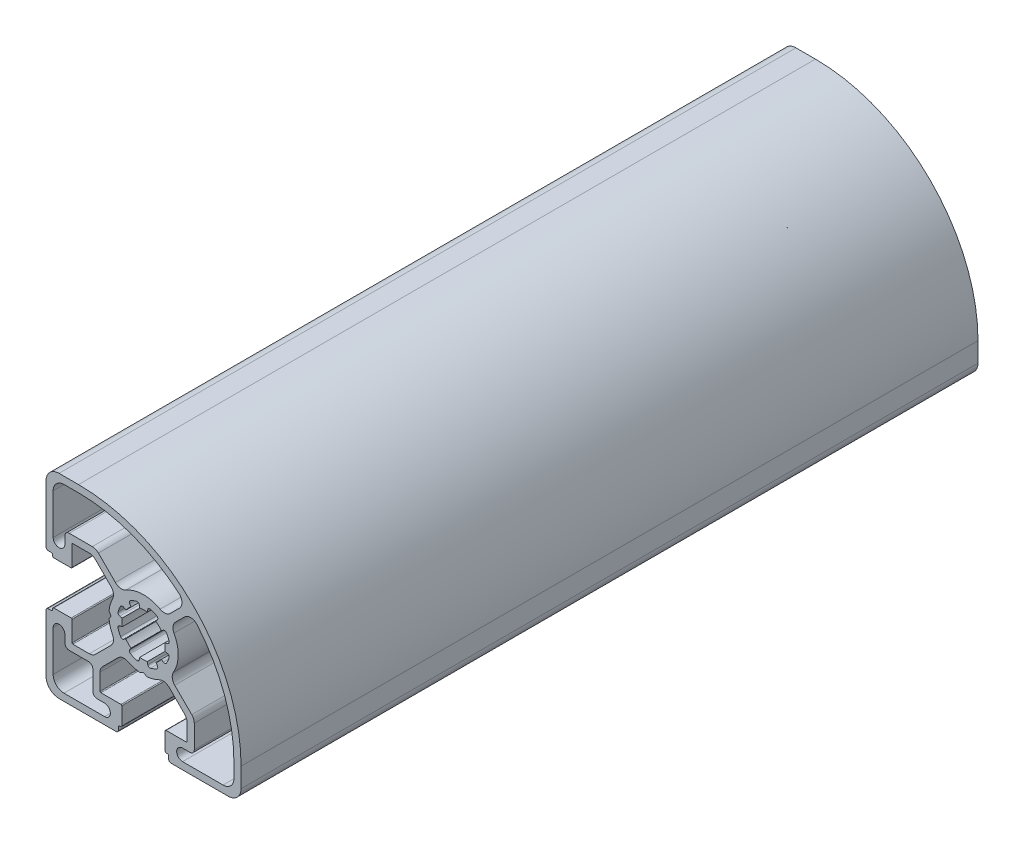
SolidWorks part; units mm, degrees
ref_plane "Front Plane" through (0, 0, 0) normal (0, 0, 1) x (1, 0, 0)
ref_plane "Top Plane" through (0, 0, 0) normal (0, 1, 0) x (1, 0, 0)
ref_plane "Right Plane" through (0, 0, 0) normal (1, 0, 0) x (0, 0, -1)
sketch "Sketch5" plane through (0, 0, 0) normal (0, 0, 1) x (1, 0, 0)
  line L0 (9.4354, 8.2687) -> (7.3664, 6.1997)
  line L1 (-22.5, 19.5) -> (-22.5, 6.3)
  line L2 (-6.493, 7.2001) -> (-10.4071, 11.1142)
  line L3 (-7.5243, 5.8979) -> (-11.0906, 9.4642)
  line L4 (-16.5, 9.85) -> (-16.5, 5.2)
  line L5 (-0.1368, -7.5833) -> (-0.7414, -7.9323)
  line L6 (-20.85, -18.35) -> (-20.85, -9)
  line L7 (-22.5, -19.5) -> (-22.5, -6.3)
  line L8 (-11.7, -17.15) -> (-11.7, -12.7)
  line L9 (-10.0399, -16.3101) -> (-10.0399, -12.5153)
  line L10 (-18.35, -20.85) -> (-9, -20.85)
  line L11 (-19.5, -22.5) -> (-6.3, -22.5)
  line L12 (-10.7, -18.15) -> (-9, -18.15)
  line L13 (-5.5, -21) -> (-5.3, -21)
  line L14 (-9.8399, -16.5101) -> (-5.2, -16.5101)
  line L15 (-5, -16.7101) -> (-5, -20.7)
  line L16 (-5.8, -22) -> (-5.8, -21.3)
  line L17 (-43.9952, 0) -> (43.9952, 0) construction
  line L18 (-18.15, -10.7) -> (-18.15, -9)
  line L19 (-21, -5.5) -> (-21, -5.3)
  line L20 (-16.7, -5) -> (-20.7, -5)
  line L21 (-16.5, -9.85) -> (-16.5, -5.2)
  line L22 (-22, -5.8) -> (-21.3, -5.8)
  line L23 (-16.3, -10.05) -> (-12.5048, -10.05)
  line L24 (-17.15, -11.7) -> (-12.7, -11.7)
  line L25 (0, 46.4479) -> (0, -46.4479) construction
  line L26 (-5.8876, -7.5346) -> (-9.4541, -11.1011)
  line L27 (-7.5243, -5.8979) -> (-11.0906, -9.4642)
  line L28 (-21, 5.3) -> (-21, 5.5)
  line L29 (-16.7, 5) -> (-20.7, 5)
  line L30 (-22, 5.8) -> (-21.3, 5.8)
  line L31 (0, 0) -> (23.3972, 0) construction
  line L32 (0, 0) -> (0, 22.9384) construction
  line L33 (0.0005, 0.0004) -> (0, 0) construction
  line L34 (-7.5577, -0.1) -> (-7.9277, -0.7409)
  line L35 (-7.5577, 0.1) -> (-7.9277, 0.7409)
  line L36 (0.0001, -0.0014) -> (0.0004, -0.001) construction
  line L37 (0.0001, -0.0002) -> (0, 0) construction
  line L38 (0.0003, -0.0003) -> (0.0001, -0.0002) construction
  line L39 (22.5, -19.5) -> (22.5, -15)
  line L40 (10.0399, -16.3101) -> (10.0399, -12.5153)
  line L41 (11.7, -17.15) -> (11.7, -11.8213)
  line L42 (20.85, -18.35) -> (20.85, -15)
  line L43 (18.35, -20.85) -> (9, -20.85)
  line L44 (10.7, -18.15) -> (9, -18.15)
  line L45 (19.5, -22.5) -> (6.3, -22.5)
  line L46 (5.3, -21.0103) -> (5.5, -21.0103)
  line L47 (9.8399, -16.5101) -> (5.2, -16.5101)
  line L48 (5, -16.7101) -> (5, -20.7103)
  line L49 (5.8, -22) -> (5.8, -21.3103)
  line L50 (0.0001, -0.0014) -> (0.0003, -0.0015) construction
  line L51 (7.2001, -6.493) -> (11.1142, -10.4071)
  line L52 (0.0632, -7.5833) -> (0.7407, -7.9744)
  line L53 (-0.8683, 4.924) -> (-0.9686, 5.4929)
  line L54 (5.9187, -7.5657) -> (9.4541, -11.1011)
  line L55 (-4.0956, 2.868) -> (-4.5688, 3.1993)
  line L56 (-2.8679, 4.0958) -> (-3.1992, 4.5689)
  line L57 (-4.924, 0.8682) -> (-5.4928, 0.9685)
  line L58 (-0.0005, -0.0004) -> (0, 0) construction
  line L59 (-0.0001, -0.0003) -> (-0.0004, -0.0007) construction
  line L60 (-0.0001, -0.0015) -> (0, -0.0017) construction
  line L61 (-20.85, 18.35) -> (-20.85, 9)
  line L62 (-18.15, 10.7) -> (-18.15, 9)
  line L63 (-17.15, 11.7) -> (-11.8213, 11.7)
  line L64 (-16.3, 10.05) -> (-12.5048, 10.05)
  line L65 (-19.5, 22.5) -> (-15, 22.5)
  line L66 (-18.35, 20.85) -> (-15, 20.85)
  line L67 (8.2687, 9.4354) -> (6.1997, 7.3664)
  line L68 (-0.0003, -0.0014) -> (-0.0001, -0.0015) construction
  line L69 (-0.0001, -0.0003) -> (-0.0003, -0.0002) construction
  line L70 (0.0001, -0.0003) -> (0.0003, -0.0002) construction
  line L71 (0.0003, -0.0014) -> (0.0001, -0.0015) construction
  line L72 (0.0001, -0.0015) -> (0, -0.0017) construction
  line L73 (0.0001, -0.0003) -> (0.0004, -0.0007) construction
  line L74 (0.0005, -0.0004) -> (0, 0) construction
  line L75 (0.8683, -4.924) -> (0.9686, -5.4929)
  line L76 (4.0956, -2.868) -> (4.5688, -3.1993)
  line L77 (-0.0001, -0.0014) -> (-0.0003, -0.0015) construction
  line L78 (-0.0003, -0.0003) -> (-0.0001, -0.0002) construction
  line L79 (2.8679, -4.0958) -> (3.1992, -4.5689)
  line L80 (4.924, -0.8682) -> (5.4928, -0.9685)
  line L81 (-4.924, -0.8682) -> (-5.4928, -0.9685)
  line L82 (-0.0001, -0.0002) -> (0, 0) construction
  line L83 (-2.8679, -4.0958) -> (-3.1992, -4.5689)
  line L84 (-4.0956, -2.868) -> (-4.5688, -3.1993)
  line L85 (-0.0001, -0.0014) -> (-0.0004, -0.001) construction
  line L86 (4.924, 0.8682) -> (5.4928, 0.9685)
  line L87 (-0.0005, 0.0004) -> (0, 0) construction
  line L88 (2.8679, 4.0958) -> (3.1992, 4.5689)
  line L89 (4.0956, 2.868) -> (4.5688, 3.1993)
  line L90 (-0.8683, -4.924) -> (-0.9686, -5.4929)
  line L91 (0.8683, 4.924) -> (0.9686, 5.4929)
  arc A0 (3.8284, 7.0245) -> (6.1997, 7.3664) centre (4.7855, 8.7806) ccw
  arc A1 (3.8284, 7.0245) -> (-4.063, 6.8914) centre (0, 0) ccw
  arc A2 (22.5, -15) -> (-15, 22.5) centre (-15, -15) ccw
  arc A3 (20.85, -15) -> (12.3769, 8.1457) centre (-15, -15) ccw
  arc A4 (-5.8887, 1.5914) -> (-5.2891, 3.0388) centre (0, 0) cw
  arc A5 (-5.2891, 3.0388) -> (-4.5688, 3.1993) centre (-4.8555, 2.7897) cw
  arc A6 (-22.5, -19.5) -> (-19.5, -22.5) centre (-19.5, -19.5) ccw
  arc A7 (-11.7, -17.15) -> (-10.7, -18.15) centre (-10.7, -17.15) ccw
  arc A8 (-20.85, -18.35) -> (-18.35, -20.85) centre (-18.35, -18.35) ccw
  arc A9 (-10.0399, -16.3101) -> (-9.8399, -16.5101) centre (-9.8399, -16.3101) ccw
  arc A10 (-5.3, -21) -> (-5, -20.7) centre (-5.3, -20.7) ccw
  arc A11 (-5.5, -21) -> (-5.8, -21.3) centre (-5.5, -21.3) ccw
  arc A12 (-5, -16.7101) -> (-5.2, -16.5101) centre (-5.2, -16.7101) ccw
  arc A13 (-9, -20.85) -> (-9, -18.15) centre (-9, -19.5) ccw
  arc A14 (-6.3, -22.5) -> (-5.8, -22) centre (-6.3, -22) ccw
  arc A15 (-7.5243, -5.8979) -> (-7.1508, -3.587) centre (-8.9385, -4.4837) ccw
  arc A16 (-12.5048, -10.05) -> (-11.0906, -9.4642) centre (-12.5048, -8.05) ccw
  arc A17 (-11.7, -12.7) -> (-12.7, -11.7) centre (-12.7, -12.7) ccw
  arc A18 (-21.3, -5.8) -> (-21, -5.5) centre (-21.3, -5.5) ccw
  arc A19 (-16.5, -9.85) -> (-16.3, -10.05) centre (-16.3, -9.85) ccw
  arc A20 (-18.15, -9) -> (-20.85, -9) centre (-19.5, -9) ccw
  arc A21 (-20.7, -5) -> (-21, -5.3) centre (-20.7, -5.3) ccw
  arc A22 (-16.5, -5.2) -> (-16.7, -5) centre (-16.7, -5.2) ccw
  arc A23 (-22, -5.8) -> (-22.5, -6.3) centre (-22, -6.3) ccw
  arc A24 (-18.15, -10.7) -> (-17.15, -11.7) centre (-17.15, -10.7) ccw
  arc A25 (-0.8629, -7.958) -> (-0.7414, -7.9323) centre (-0.8414, -7.7591) ccw
  arc A26 (-1.5914, 5.8888) -> (-0.9686, 5.4929) centre (-1.461, 5.4061) cw
  arc A27 (-3.5791, -7.1599) -> (-0.8629, -7.958) centre (0, 0) ccw
  arc A28 (-4.0956, 2.868) -> (-2.8679, 4.0958) centre (0, 0) cw
  arc A29 (-4.924, -0.8682) -> (-4.924, 0.8682) centre (0, 0) cw
  arc A30 (-3.5791, -7.1599) -> (-5.8876, -7.5346) centre (-4.4734, -8.9488) ccw
  arc A31 (-9.4541, -11.1011) -> (-10.0399, -12.5153) centre (-8.0399, -12.5153) ccw
  arc A32 (-21, 5.5) -> (-21.3, 5.8) centre (-21.3, 5.5) ccw
  arc A33 (-21, 5.3) -> (-20.7, 5) centre (-20.7, 5.3) ccw
  arc A34 (-16.7, 5) -> (-16.5, 5.2) centre (-16.7, 5.2) ccw
  arc A35 (-22.5, 6.3) -> (-22, 5.8) centre (-22, 6.3) ccw
  arc A36 (-5.4928, 0.9685) -> (-5.8887, 1.5914) centre (-5.406, 1.4609) cw
  arc A37 (-3.0387, 5.2893) -> (-1.5914, 5.8888) centre (0, 0) cw
  arc A38 (-3.1992, 4.5689) -> (-3.0387, 5.2893) centre (-2.7896, 4.8557) cw
  arc A39 (5.8887, -1.5914) -> (5.2891, -3.0388) centre (0, 0) cw
  arc A40 (5.2891, -3.0388) -> (4.5688, -3.1993) centre (4.8555, -2.7897) cw
  arc A41 (1.5914, -5.8888) -> (0.9686, -5.4929) centre (1.461, -5.4061) cw
  arc A42 (-6.493, 7.2001) -> (-4.063, 6.8914) centre (-5.0788, 8.6143) ccw
  arc A43 (-7.1508, 3.587) -> (-7.5243, 5.8979) centre (-8.9385, 4.4837) ccw
  arc A44 (-7.9534, -0.8624) -> (-7.1508, -3.587) centre (0, 0) ccw
  arc A45 (4.0956, -2.868) -> (2.8679, -4.0958) centre (0, 0) cw
  arc A46 (-7.5577, -0.1) -> (-7.5577, 0.1) centre (-7.7309, 0) ccw
  arc A47 (-7.9534, 0.8625) -> (-7.9277, 0.7409) centre (-7.7545, 0.8409) ccw
  arc A48 (-7.9277, -0.7409) -> (-7.9534, -0.8624) centre (-7.7545, -0.8409) ccw
  arc A49 (5.4928, -0.9685) -> (5.8887, -1.5914) centre (5.406, -1.4609) cw
  arc A50 (3.0387, -5.2893) -> (1.5914, -5.8888) centre (0, 0) cw
  arc A51 (3.1992, -4.5689) -> (3.0387, -5.2893) centre (2.7896, -4.8557) cw
  arc A52 (0.8683, -4.924) -> (-0.8683, -4.924) centre (0, 0) cw
  arc A53 (-7.1508, 3.587) -> (-7.9534, 0.8625) centre (0, 0) ccw
  arc A54 (-3.1992, -4.5689) -> (-3.0387, -5.2893) centre (-2.7896, -4.8557) ccw
  arc A55 (19.5, -22.5) -> (22.5, -19.5) centre (19.5, -19.5) ccw
  arc A56 (5.8, -21.3103) -> (5.5, -21.0103) centre (5.5, -21.3103) ccw
  arc A57 (5, -20.7103) -> (5.3, -21.0103) centre (5.3, -20.7103) ccw
  arc A58 (5.2, -16.5101) -> (5, -16.7101) centre (5.2, -16.7101) ccw
  arc A59 (9, -18.15) -> (9, -20.85) centre (9, -19.5) ccw
  arc A60 (9.8399, -16.5101) -> (10.0399, -16.3101) centre (9.8399, -16.3101) ccw
  arc A61 (5.8, -22) -> (6.3, -22.5) centre (6.3, -22) ccw
  arc A62 (10.7, -18.15) -> (11.7, -17.15) centre (10.7, -17.15) ccw
  arc A63 (18.35, -20.85) -> (20.85, -18.35) centre (18.35, -18.35) ccw
  arc A64 (6.8914, -4.063) -> (7.2001, -6.493) centre (8.6143, -5.0788) ccw
  arc A65 (-3.0387, -5.2893) -> (-1.5914, -5.8888) centre (0, 0) ccw
  arc A66 (0.8621, -8) -> (3.6077, -7.1922) centre (0, 0) ccw
  arc A67 (-5.4928, -0.9685) -> (-5.8887, -1.5914) centre (-5.406, -1.4609) ccw
  arc A68 (-4.0956, -2.868) -> (-2.8679, -4.0958) centre (0, 0) ccw
  arc A69 (5.9187, -7.5657) -> (3.6077, -7.1922) centre (4.5045, -8.9799) ccw
  arc A70 (0.7407, -7.9744) -> (0.8621, -8) centre (0.8407, -7.8012) ccw
  arc A71 (0.0632, -7.5833) -> (-0.1368, -7.5833) centre (-0.0368, -7.7565) ccw
  arc A72 (10.0399, -12.5153) -> (9.4541, -11.1011) centre (8.0399, -12.5153) ccw
  arc A73 (11.7, -11.8213) -> (11.1142, -10.4071) centre (9.7, -11.8213) ccw
  arc A74 (-1.5914, -5.8888) -> (-0.9686, -5.4929) centre (-1.461, -5.4061) ccw
  arc A75 (-5.2891, -3.0388) -> (-4.5688, -3.1993) centre (-4.8555, -2.7897) ccw
  arc A76 (-5.8887, -1.5914) -> (-5.2891, -3.0388) centre (0, 0) ccw
  arc A77 (0.8683, 4.924) -> (-0.8683, 4.924) centre (0, 0) ccw
  arc A78 (3.1992, 4.5689) -> (3.0387, 5.2893) centre (2.7896, 4.8557) ccw
  arc A79 (3.0387, 5.2893) -> (1.5914, 5.8888) centre (0, 0) ccw
  arc A80 (7.3664, 6.1997) -> (7.0245, 3.8284) centre (8.7806, 4.7855) ccw
  arc A81 (5.4928, 0.9685) -> (5.8887, 1.5914) centre (5.406, 1.4609) ccw
  arc A82 (4.924, -0.8682) -> (4.924, 0.8682) centre (0, 0) ccw
  arc A83 (4.0956, 2.868) -> (2.8679, 4.0958) centre (0, 0) ccw
  arc A84 (1.5914, 5.8888) -> (0.9686, 5.4929) centre (1.461, 5.4061) ccw
  arc A85 (5.2891, 3.0388) -> (4.5688, 3.1993) centre (4.8555, 2.7897) ccw
  arc A86 (6.8914, -4.063) -> (7.0245, 3.8284) centre (0, 0) ccw
  arc A87 (5.8887, 1.5914) -> (5.2891, 3.0388) centre (0, 0) ccw
  arc A88 (8.1457, 12.3769) -> (-15, 20.85) centre (-15, -15) ccw
  arc A89 (-19.5, 22.5) -> (-22.5, 19.5) centre (-19.5, 19.5) ccw
  arc A90 (-18.35, 20.85) -> (-20.85, 18.35) centre (-18.35, 18.35) ccw
  arc A91 (-10.4071, 11.1142) -> (-11.8213, 11.7) centre (-11.8213, 9.7) ccw
  arc A92 (-11.0906, 9.4642) -> (-12.5048, 10.05) centre (-12.5048, 8.05) ccw
  arc A93 (-17.15, 11.7) -> (-18.15, 10.7) centre (-17.15, 10.7) ccw
  arc A94 (-20.85, 9) -> (-18.15, 9) centre (-19.5, 9) ccw
  arc A95 (-16.3, 10.05) -> (-16.5, 9.85) centre (-16.3, 9.85) ccw
  arc A96 (12.3769, 8.1457) -> (9.4354, 8.2687) centre (10.8496, 6.8545) ccw
  arc A97 (8.2687, 9.4354) -> (8.1457, 12.3769) centre (6.8545, 10.8496) ccw
  dimension "D5" = 37.5
  dimension "D6" = 10
  dimension "D1" = 45
  dimension "D2" = 45
  dimension "D3" = 22.5
  dimension "D4" = 10
  dimension "D7" = 14.5
extrude "Extrude1" add sketch "Sketch5" against normal blind 170
